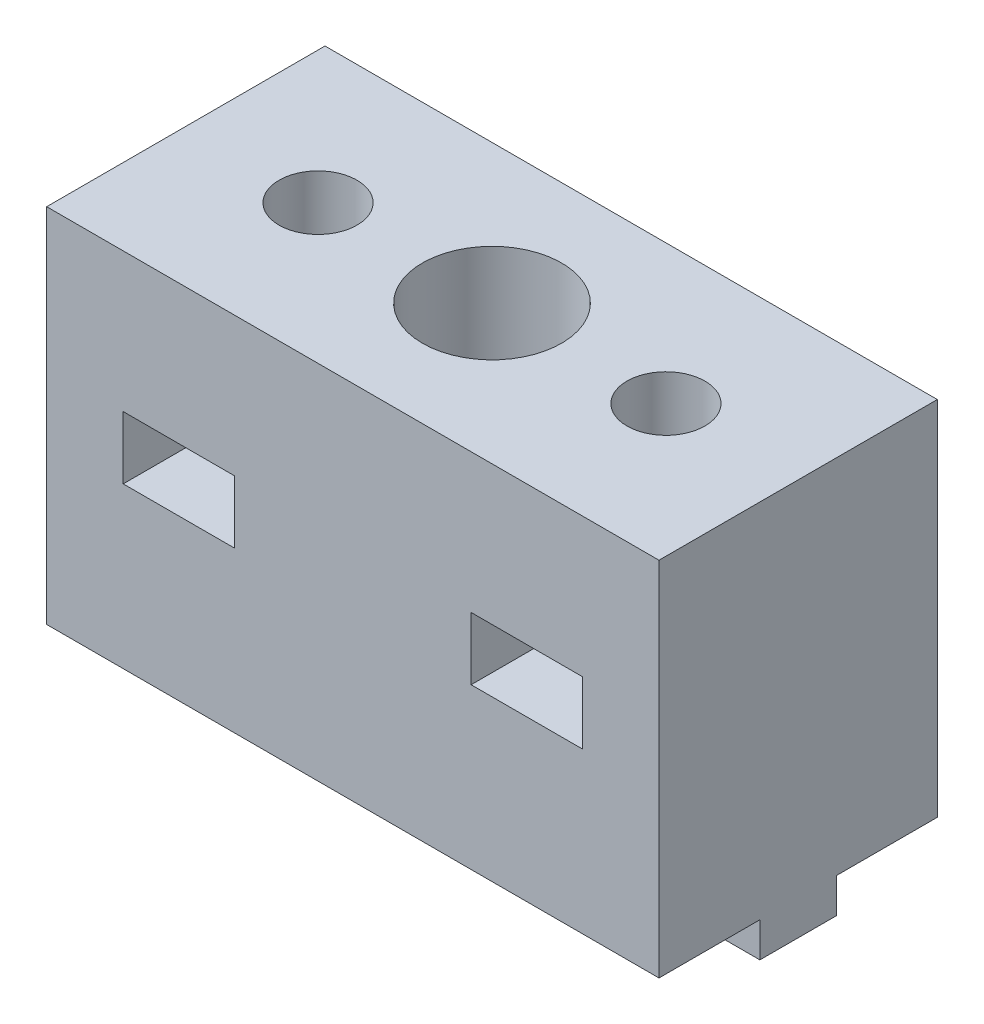
SolidWorks part; units mm, degrees
ref_plane "Front Plane" through (0, 0, 0) normal (0, 0, 1) x (1, 0, 0)
ref_plane "Top Plane" through (0, 0, 0) normal (0, 1, 0) x (1, 0, 0)
ref_plane "Right Plane" through (0, 0, 0) normal (1, 0, 0) x (0, 0, -1)
sketch "Sketch1" plane through (0, 0, 0) normal (0, 1, 0) x (1, 0, 0)
  line L1 (-0.6968, 0) -> (43.3032, 0)
  line L2 (-0.6968, 0) -> (-0.6968, 20)
  line L3 (-0.6968, 20) -> (43.3032, 20)
  line L4 (43.3032, 0) -> (43.3032, 20)
  dimension "D1" = 20
  dimension "D2" = 44
extrude "Boss-Extrude1" add sketch "Sketch1" along normal blind 26
sketch "Sketch3" plane through (0, 0, 0) normal (0, -1, 0) x (1, 0, 0)
  line L0 (43.3032, 0) -> (43.3032, -20) construction
  line L1 (43.3032, -12.75) -> (-0.6968, -12.75)
  line L2 (43.3032, -12.75) -> (43.3032, -7.25)
  line L3 (43.3032, -7.25) -> (-0.6968, -7.25)
  line L4 (-0.6968, -12.75) -> (-0.6968, -7.25)
  line L5 (-0.6968, -20) -> (-0.6968, 0) construction
  line L6 (43.3032, -20) -> (-0.6968, -20) construction
  dimension "D1" = 5.5
  dimension "D2" = 7.25
extrude "Boss-Extrude5" add sketch "Sketch3" along normal blind 2.5
sketch "Sketch2" plane through (0, 26, 0) normal (0, 1, 0) x (1, 0, 0)
  line L0 (43.3032, 20) -> (-0.6968, 20) construction
  line L1 (-0.6968, 20) -> (-0.6968, 0) construction
  line L2 (43.3032, 0) -> (43.3032, 20) construction
  circle A0 centre (8.8032, 10) radius 2.8
  circle A1 centre (33.8032, 10) radius 2.8
  circle A2 centre (21.3032, 10) radius 2.8
  dimension "D1" = 5.6
  dimension "D2" = 5.6
  dimension "D3" = 5.6
  dimension "D4" = 22
  dimension "D5" = 10
  dimension "D6" = 10
  dimension "D7" = 25
  dimension "D9" = 9.5
extrude "Cut-Extrude1" cut sketch "Sketch2" against normal through all
sketch "Sketch4" plane through (0, 26, 0) normal (0, 1, 0) x (1, 0, 0)
  line L0 (-0.6968, 0) -> (43.3032, 0) construction
  line L1 (-0.6968, 20) -> (-0.6968, 0) construction
  circle A0 centre (21.3032, 10) radius 5
  dimension "D1" = 10
  dimension "D2" = 10
  dimension "D3" = 22
extrude "Cut-Extrude2" cut sketch "Sketch4" against normal offset from surface (21 mm away) 5 up to face at (21.3032, 0, -5.785)
sketch "Sketch5" plane through (0, 0, -20) normal (0, 0, -1) x (-1, 0, 0)
  line L1 (-37.8032, 11.5) -> (-29.8032, 11.5)
  line L2 (-37.8032, 11.5) -> (-37.8032, 16)
  line L3 (-37.8032, 16) -> (-29.8032, 16)
  line L4 (-29.8032, 11.5) -> (-29.8032, 16)
  line L5 (-12.8032, 11.5) -> (-4.8032, 11.5)
  line L6 (-12.8032, 11.5) -> (-12.8032, 16)
  line L7 (-12.8032, 16) -> (-4.8032, 16)
  line L8 (-4.8032, 11.5) -> (-4.8032, 16)
  line L9 (-43.3032, 26) -> (0.6968, 26) construction
  line L10 (-43.3032, 26) -> (-43.3032, 0) construction
  line L11 (0.6968, 26) -> (0.6968, 0) construction
  dimension "D1" = 4.5
  dimension "D2" = 8
  dimension "D3" = 4.5
  dimension "D4" = 8
  dimension "D5" = 10
  dimension "D6" = 10
  dimension "D7" = 5.5
  dimension "D8" = 5.5
extrude "Cut-Extrude3" cut sketch "Sketch5" against normal through all
sketch "Sketch6" plane through (0, -2.5, 0) normal (0, -1, 0) x (1, 0, 0)
  line L0 (33.2765, -7.25) -> (21.83, -7.25) construction
  line L1 (26.3032, -7.25) -> (16.3032, -7.25)
  line L2 (26.3032, -7.25) -> (26.3032, -12.75)
  line L3 (26.3032, -12.75) -> (16.3032, -12.75)
  line L4 (16.3032, -7.25) -> (16.3032, -12.75)
  arc A0 (21.83, -12.75) -> (21.83, -7.25) centre (21.3032, -10) ccw construction
  arc A2 (20.7765, -7.25) -> (20.7765, -12.75) centre (21.3032, -10) ccw construction
  dimension "D1" = 5
  dimension "D2" = 5
extrude "Cut-Extrude4" cut sketch "Sketch6" against normal up to surface (2.5 mm away) up to face at (21.3032, 0, -14.215)
